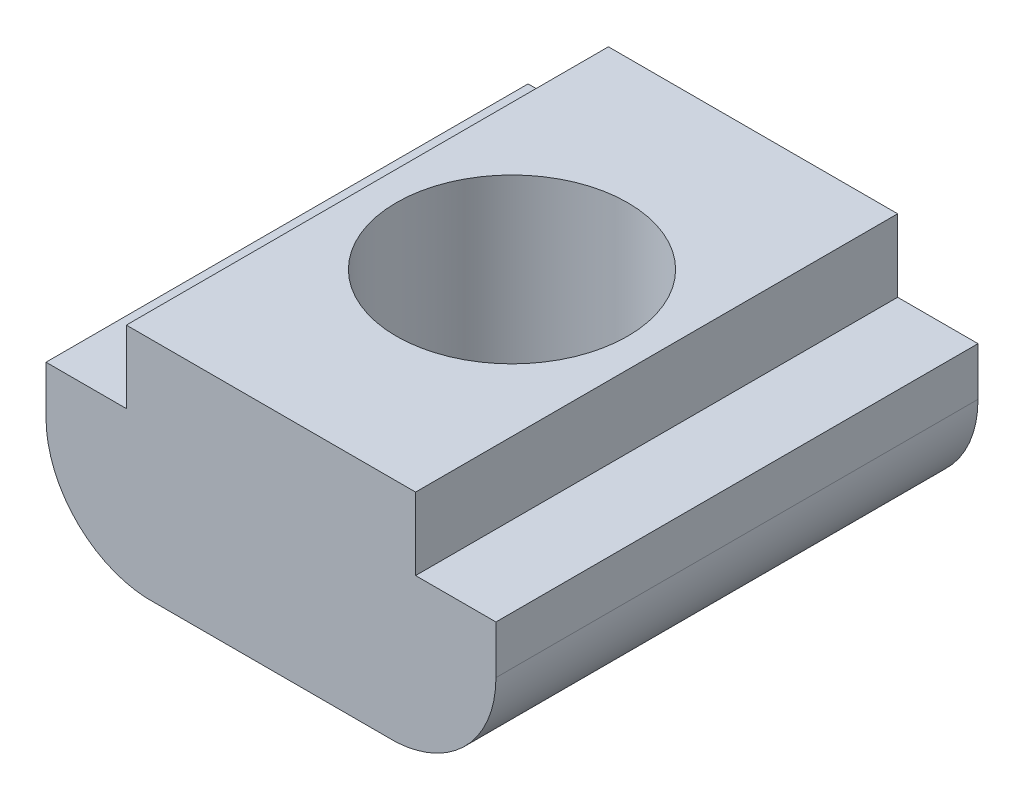
SolidWorks part; units mm, degrees
ref_plane "前视基准面" through (0, 0, 0) normal (0, 0, 1) x (1, 0, 0)
ref_plane "上视基准面" through (0, 0, 0) normal (0, 1, 0) x (1, 0, 0)
ref_plane "右视基准面" through (0, 0, 0) normal (1, 0, 0) x (0, 0, -1)
sketch "草图1" plane through (0, 0, 0) normal (0, 0, 1) x (1, 0, 0)
  line L0 (3, 3) -> (-3, 3)
  line L1 (0, 3) -> (0, -1.6938) construction
  line L2 (-3, 3) -> (-3, 1.5)
  line L3 (4.6667, 1.5) -> (-4.6667, 1.5) construction
  line L4 (-3, 1.5) -> (-4.6667, 1.5)
  line L5 (2.6, -1.6938) -> (-2.6, -1.6938)
  line L6 (-4.6667, 1.5) -> (-4.6667, 0.5)
  line L7 (3, 3) -> (3, 1.5)
  line L8 (3, 1.5) -> (4.6667, 1.5)
  line L9 (4.6667, 1.5) -> (4.6667, 0.5)
  arc A0 (-4.6667, 0.5) -> (-2.6, -1.6938) centre (-2.4691, 0.5) ccw
  arc A1 (4.6667, 0.5) -> (2.6, -1.6938) centre (2.4691, 0.5) cw
  point P8 (0, 1.5)
  point P17 (0, -1.6938)
extrude "凸台-拉伸1" add sketch "草图1" along normal blind 10
hole_wizard "M6 螺纹孔4" positions "草图12" profile "草图13" tap size "M6" standard "ISO" end condition through all
sketch "草图12" plane through (0, 3, 0) normal (0, 1, 0) x (1, 0, 0)
  point P0 (0, -5)
sketch "草图13" plane through (0, 3, 5) normal (1, 0, 0) x (0, 0, 1)
  line L0 (0, 0) -> (0, 4.6938)
  line L1 (0, 4.6938) -> (2.4, 4.6938)
  line L2 (2.4, 4.6938) -> (2.4, 0)
  line L5 (2.4, 0) -> (0, 0)
  line L11 (0, -6.35) -> (0, 107.95) construction
  dimension "通孔螺纹孔钻头直径" = 4.8
  dimension "通孔螺纹孔钻头深度" = 4.6938
cosmetic thread "孔螺蚊线4" parameters "D2"=6
move or copy body "实体-移动/复制1" bodies to move or copy 107 copy no translate (0, 0, -5)
